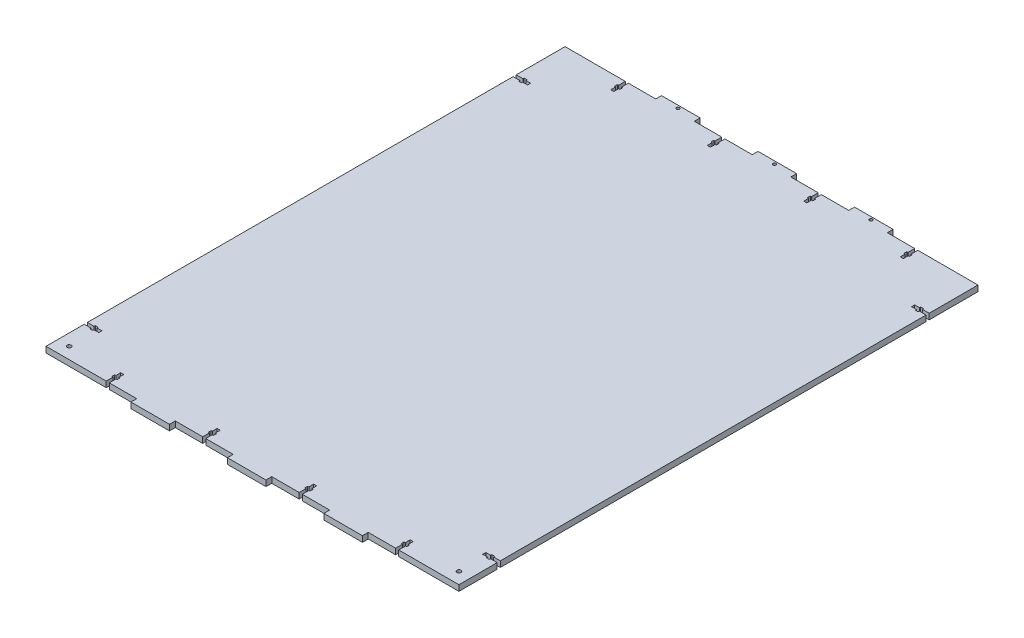
SolidWorks part; units mm, degrees
ref_plane "Front Plane" through (0, 0, 0) normal (0, 0, 1) x (1, 0, 0)
ref_plane "Top Plane" through (0, 0, 0) normal (0, 1, 0) x (1, 0, 0)
ref_plane "Right Plane" through (0, 0, 0) normal (1, 0, 0) x (0, 0, -1)
sketch "Sketch1" plane through (0, 0, 0) normal (0, 1, 0) x (1, 0, 0)
  line L1 (-214, -269) -> (214, -269)
  line L2 (-214, -269) -> (-214, 269)
  line L3 (-214, 269) -> (214, 269)
  line L4 (214, -269) -> (214, 269)
  line L5 (-214, -269) -> (214, 269) construction
  line L6 (-214, 269) -> (214, -269) construction
  point P0 (0, 0)
  dimension "D1" = 428
  dimension "D2" = 538
extrude "Boss-Extrude1" add sketch "Sketch1" along normal blind 6
sketch "Sketch2" plane through (0, 0, 0) normal (0, -1, 0) x (1, 0, 0)
  line L14 (0, 0) -> (0, 133.2527) construction
  line L15 (0, 0) -> (-145.1849, 0) construction
  line L40 (-148.4, 275) -> (-151.6, 275) construction
  line L41 (-148.4, 275) -> (-151.6, 275) construction
  line L42 (-48.4, 275) -> (-51.6, 275) construction
  line L43 (-48.4, 275) -> (-51.6, 275) construction
  line L44 (-148.4, 275) -> (-51.6, 275) construction
  line L45 (-214, 269) -> (214, 269) construction
  line L46 (-120, 275) -> (-80, 275)
  line L47 (-120, 275) -> (-120, 269)
  line L48 (-120, 269) -> (-80, 269)
  line L49 (-80, 275) -> (-80, 269)
  line L50 (-20, 269) -> (20, 269)
  line L51 (20, 275) -> (20, 269)
  line L52 (-20, 275) -> (20, 275)
  line L53 (-20, 275) -> (-20, 269)
  line L54 (80, 269) -> (120, 269)
  line L55 (120, 275) -> (120, 269)
  line L56 (80, 275) -> (120, 275)
  line L57 (80, 275) -> (80, 269)
  line L58 (120, -275) -> (120, -269)
  line L59 (80, -269) -> (120, -269)
  line L60 (80, -275) -> (120, -275)
  line L61 (80, -275) -> (80, -269)
  line L62 (20, -275) -> (20, -269)
  line L63 (-20, -275) -> (20, -275)
  line L64 (-20, -269) -> (20, -269)
  line L65 (-20, -275) -> (-20, -269)
  line L66 (-120, -269) -> (-80, -269)
  line L67 (-120, -275) -> (-120, -269)
  line L68 (-120, -275) -> (-80, -275)
  line L69 (-80, -275) -> (-80, -269)
  point P50 (-100, 275)
  dimension "D3" = 40
  dimension "D4" = 3
extrude "Boss-Extrude2" add sketch "Sketch2" against normal blind 6
sketch "Sketch3" plane through (0, 0, 0) normal (0, -1, 0) x (1, 0, 0)
  line L0 (207, -219.55) -> (207, -218.35)
  line L1 (-214, -218.35) -> (-214, -215.15) construction
  line L2 (-214, -218.35) -> (-214, -215.15) construction
  line L3 (207, -219.55) -> (204, -219.55)
  line L4 (204, -219.55) -> (204, -218.35)
  line L5 (204, -218.35) -> (199, -218.35)
  line L6 (-214, 226.15) -> (-214, 229.35) construction
  line L7 (-214, 226.15) -> (-214, 229.35) construction
  line L8 (-214, -216.75) -> (-199, -216.75) construction
  line L9 (-214, 227.75) -> (-199, 227.75) construction
  line L10 (-214, 226.15) -> (-207, 226.15)
  line L11 (-214, -218.35) -> (-207, -218.35)
  line L12 (-214, 229.35) -> (-207, 229.35)
  line L13 (-214, -215.15) -> (-207, -215.15)
  line L14 (-214, 226.15) -> (-214, 229.35)
  line L15 (-199, 226.15) -> (-199, 229.35)
  line L16 (-214, -218.35) -> (-214, -215.15)
  line L17 (-199, -218.35) -> (-199, -215.15)
  line L18 (-207, 229.35) -> (-207, 230.55)
  line L19 (-207, -219.55) -> (-204, -219.55)
  line L20 (-207, -219.55) -> (-207, -218.35)
  line L21 (-207, -213.95) -> (-204, -213.95)
  line L22 (199, -218.35) -> (199, -215.15)
  line L23 (-204, -219.55) -> (-204, -218.35)
  line L24 (-207, -219.55) -> (-204, -213.95) construction
  line L25 (-207, -213.95) -> (-204, -219.55) construction
  line L26 (-207, 224.95) -> (-204, 224.95)
  line L27 (-207, 224.95) -> (-207, 226.15)
  line L28 (-207, 230.55) -> (-204, 230.55)
  line L29 (-204, 224.95) -> (-204, 226.15)
  line L30 (-207, 224.95) -> (-204, 230.55) construction
  line L31 (-207, 230.55) -> (-204, 224.95) construction
  line L32 (-204, 229.35) -> (-199, 229.35)
  line L33 (-214, 229.35) -> (-199, 229.35) construction
  line L34 (-204, 226.15) -> (-199, 226.15)
  line L35 (-214, 226.15) -> (-199, 226.15) construction
  line L36 (-204, 229.35) -> (-204, 230.55)
  line L37 (-204, -215.15) -> (-204, -213.95)
  line L38 (-204, -218.35) -> (-199, -218.35)
  line L39 (-214, -218.35) -> (-199, -218.35) construction
  line L40 (-207, -215.15) -> (-207, -213.95)
  line L41 (-204, -215.15) -> (-199, -215.15)
  line L42 (-214, -215.15) -> (-199, -215.15) construction
  line L43 (204, -215.15) -> (199, -215.15)
  line L44 (204, -215.15) -> (204, -213.95)
  line L45 (207, -213.95) -> (204, -213.95)
  line L46 (207, -215.15) -> (207, -213.95)
  line L47 (214, -215.15) -> (207, -215.15)
  line L48 (214, -218.35) -> (214, -215.15)
  line L49 (214, -218.35) -> (207, -218.35)
  line L50 (214, 226.15) -> (207, 226.15)
  line L51 (207, 224.95) -> (207, 226.15)
  line L52 (207, 224.95) -> (204, 224.95)
  line L53 (204, 224.95) -> (204, 226.15)
  line L54 (204, 226.15) -> (199, 226.15)
  line L55 (199, 226.15) -> (199, 229.35)
  line L56 (204, 229.35) -> (199, 229.35)
  line L57 (204, 229.35) -> (204, 230.55)
  line L58 (207, 230.55) -> (204, 230.55)
  line L59 (207, 229.35) -> (207, 230.55)
  line L60 (214, 226.15) -> (214, 229.35)
  line L61 (214, 229.35) -> (207, 229.35)
  line L62 (-120, -272) -> (-80, -272) construction
  line L63 (0, 0) -> (160.2761, 0) construction
  line L64 (147.2, 259) -> (152.8, 262) construction
  line L65 (-120, -269) -> (-120, -275) construction
  line L66 (-80, -275) -> (-80, -269) construction
  line L67 (147.2, 262) -> (152.8, 259) construction
  line L68 (148.4, 269) -> (151.6, 254) construction
  line L69 (148.4, 254) -> (151.6, 269) construction
  line L70 (47.2, 259) -> (52.8, 262) construction
  line L71 (47.2, 262) -> (52.8, 259) construction
  line L72 (48.4, 269) -> (51.6, 254) construction
  line L73 (48.4, 254) -> (51.6, 269) construction
  line L74 (151.6, 259) -> (152.8, 259)
  line L75 (151.6, 262) -> (151.6, 269)
  line L76 (148.4, 262) -> (148.4, 269)
  line L77 (152.8, 262) -> (152.8, 259)
  line L78 (147.2, 259) -> (148.4, 259)
  line L79 (147.2, 262) -> (147.2, 259)
  line L80 (147.2, 262) -> (148.4, 262)
  line L81 (151.6, 262) -> (152.8, 262)
  line L82 (151.6, 254) -> (151.6, 259)
  line L83 (148.4, 269) -> (151.6, 269)
  line L84 (148.4, 254) -> (148.4, 259)
  line L85 (148.4, 254) -> (151.6, 254)
  line L86 (0, 0) -> (0, 128.8409) construction
  line L87 (51.6, 259) -> (52.8, 259)
  line L88 (51.6, 262) -> (51.6, 269)
  line L89 (48.4, 262) -> (48.4, 269)
  line L90 (52.8, 262) -> (52.8, 259)
  line L91 (47.2, 259) -> (48.4, 259)
  line L92 (47.2, 262) -> (47.2, 259)
  line L93 (47.2, 262) -> (48.4, 262)
  line L94 (51.6, 262) -> (52.8, 262)
  line L95 (51.6, 254) -> (51.6, 259)
  line L96 (48.4, 269) -> (51.6, 269)
  line L97 (48.4, 254) -> (48.4, 259)
  line L98 (48.4, 254) -> (51.6, 254)
  line L99 (-52.8, 259) -> (-47.2, 262) construction
  line L100 (-52.8, 262) -> (-47.2, 259) construction
  line L101 (-51.6, 269) -> (-48.4, 254) construction
  line L102 (-51.6, 254) -> (-48.4, 269) construction
  line L103 (-152.8, 259) -> (-147.2, 262) construction
  line L104 (-152.8, 262) -> (-147.2, 259) construction
  line L105 (-151.6, 269) -> (-148.4, 254) construction
  line L106 (-151.6, 254) -> (-148.4, 269) construction
  line L107 (-48.4, 259) -> (-47.2, 259)
  line L108 (-48.4, 262) -> (-48.4, 269)
  line L109 (-51.6, 262) -> (-51.6, 269)
  line L110 (-47.2, 262) -> (-47.2, 259)
  line L111 (-52.8, 259) -> (-51.6, 259)
  line L112 (-52.8, 262) -> (-52.8, 259)
  line L113 (-52.8, 262) -> (-51.6, 262)
  line L114 (-48.4, 262) -> (-47.2, 262)
  line L115 (-48.4, 254) -> (-48.4, 259)
  line L116 (-51.6, 269) -> (-48.4, 269)
  line L117 (-51.6, 254) -> (-51.6, 259)
  line L118 (-51.6, 254) -> (-48.4, 254)
  line L119 (-148.4, 259) -> (-147.2, 259)
  line L120 (-148.4, 262) -> (-148.4, 269)
  line L121 (-151.6, 262) -> (-151.6, 269)
  line L122 (-147.2, 262) -> (-147.2, 259)
  line L123 (-152.8, 259) -> (-151.6, 259)
  line L124 (-152.8, 262) -> (-152.8, 259)
  line L125 (-152.8, 262) -> (-151.6, 262)
  line L126 (-148.4, 262) -> (-147.2, 262)
  line L127 (-148.4, 254) -> (-148.4, 259)
  line L128 (-151.6, 269) -> (-148.4, 269)
  line L129 (-151.6, 254) -> (-151.6, 259)
  line L130 (-151.6, 254) -> (-148.4, 254)
  line L166 (-151.6, -275) -> (-148.4, -275) construction
  line L167 (-151.6, -275) -> (-148.4, -275) construction
  line L168 (-150, -275) -> (-150, -234.6121) construction
  line L169 (-120, -269) -> (-214, -269) construction
  line L170 (-151.6, -254) -> (-148.4, -254)
  line L171 (-151.6, -254) -> (-151.6, -259)
  line L172 (-151.6, -269) -> (-148.4, -269)
  line L173 (-148.4, -254) -> (-148.4, -259)
  line L174 (-151.6, -254) -> (-148.4, -269) construction
  line L175 (-151.6, -269) -> (-148.4, -254) construction
  line L176 (-148.4, -262) -> (-147.2, -262)
  line L177 (-152.8, -262) -> (-151.6, -262)
  line L178 (-152.8, -262) -> (-152.8, -259)
  line L179 (-152.8, -259) -> (-151.6, -259)
  line L180 (-147.2, -262) -> (-147.2, -259)
  line L181 (-152.8, -262) -> (-147.2, -259) construction
  line L182 (-152.8, -259) -> (-147.2, -262) construction
  line L183 (-151.6, -262) -> (-151.6, -269)
  line L184 (-148.4, -262) -> (-148.4, -269)
  line L185 (-148.4, -259) -> (-147.2, -259)
  line L186 (-51.6, -254) -> (-48.4, -254)
  line L187 (-51.6, -254) -> (-51.6, -259)
  line L188 (-51.6, -269) -> (-48.4, -269)
  line L189 (-48.4, -254) -> (-48.4, -259)
  line L190 (-48.4, -262) -> (-47.2, -262)
  line L191 (-52.8, -262) -> (-51.6, -262)
  line L192 (-52.8, -262) -> (-52.8, -259)
  line L193 (-52.8, -259) -> (-51.6, -259)
  line L194 (-47.2, -262) -> (-47.2, -259)
  line L195 (-51.6, -262) -> (-51.6, -269)
  line L196 (-48.4, -262) -> (-48.4, -269)
  line L197 (-48.4, -259) -> (-47.2, -259)
  line L198 (-51.6, -254) -> (-48.4, -269) construction
  line L199 (-51.6, -269) -> (-48.4, -254) construction
  line L200 (-52.8, -262) -> (-47.2, -259) construction
  line L201 (-52.8, -259) -> (-47.2, -262) construction
  line L202 (48.4, -254) -> (51.6, -254)
  line L203 (48.4, -254) -> (48.4, -259)
  line L204 (48.4, -269) -> (51.6, -269)
  line L205 (51.6, -254) -> (51.6, -259)
  line L206 (51.6, -262) -> (52.8, -262)
  line L207 (47.2, -262) -> (48.4, -262)
  line L208 (47.2, -262) -> (47.2, -259)
  line L209 (47.2, -259) -> (48.4, -259)
  line L210 (52.8, -262) -> (52.8, -259)
  line L211 (48.4, -262) -> (48.4, -269)
  line L212 (51.6, -262) -> (51.6, -269)
  line L213 (51.6, -259) -> (52.8, -259)
  line L214 (48.4, -254) -> (51.6, -269) construction
  line L215 (48.4, -269) -> (51.6, -254) construction
  line L216 (47.2, -262) -> (52.8, -259) construction
  line L217 (47.2, -259) -> (52.8, -262) construction
  line L218 (148.4, -254) -> (151.6, -254)
  line L219 (148.4, -254) -> (148.4, -259)
  line L220 (148.4, -269) -> (151.6, -269)
  line L221 (151.6, -254) -> (151.6, -259)
  line L222 (151.6, -262) -> (152.8, -262)
  line L223 (147.2, -262) -> (148.4, -262)
  line L224 (147.2, -262) -> (147.2, -259)
  line L225 (147.2, -259) -> (148.4, -259)
  line L226 (152.8, -262) -> (152.8, -259)
  line L227 (148.4, -262) -> (148.4, -269)
  line L228 (151.6, -262) -> (151.6, -269)
  line L229 (151.6, -259) -> (152.8, -259)
  line L230 (148.4, -254) -> (151.6, -269) construction
  line L231 (148.4, -269) -> (151.6, -254) construction
  line L232 (147.2, -262) -> (152.8, -259) construction
  line L233 (147.2, -259) -> (152.8, -262) construction
  circle A0 centre (-100, -272) radius 1.6
  circle A1 centre (0, -272) radius 1.6
  circle A2 centre (100, -272) radius 1.6
  circle A4 centre (202, 257) radius 2.1 construction
  circle A5 centre (202, 257) radius 2.1
  circle A6 centre (-202, 257) radius 2.1 construction
  circle A7 centre (-202, 257) radius 2.1
  point P25 (-205.5, -216.75)
  point P30 (-205.5, 227.75)
  point P104 (150, 260.5)
  point P105 (150, 261.5)
  point P106 (50, 260.5)
  point P107 (50, 261.5)
  point P132 (-50, 260.5)
  point P133 (-50, 261.5)
  point P134 (-150, 260.5)
  point P135 (-150, 261.5)
  point P154 (-150, -261.5)
  point P161 (-150, -260.5)
  point P171 (-50, -261.5)
  point P176 (-50, -260.5)
  point P185 (50, -261.5)
  point P190 (50, -260.5)
  point P199 (150, -261.5)
  point P204 (150, -260.5)
  dimension "D11" = 3.2
  dimension "D1" = 15
  dimension "D2" = 1.6
  dimension "D3" = 1.6
  dimension "D4" = 7
  dimension "D5" = 5.6
  dimension "D6" = 15
  dimension "D7" = 5.6
  dimension "D8" = 7
  dimension "D10" = 3
  dimension "D13" = 3
  dimension "D9" = 4
  dimension "D12" = 3
extrude "Cut-Extrude1" cut sketch "Sketch3" against normal through all
